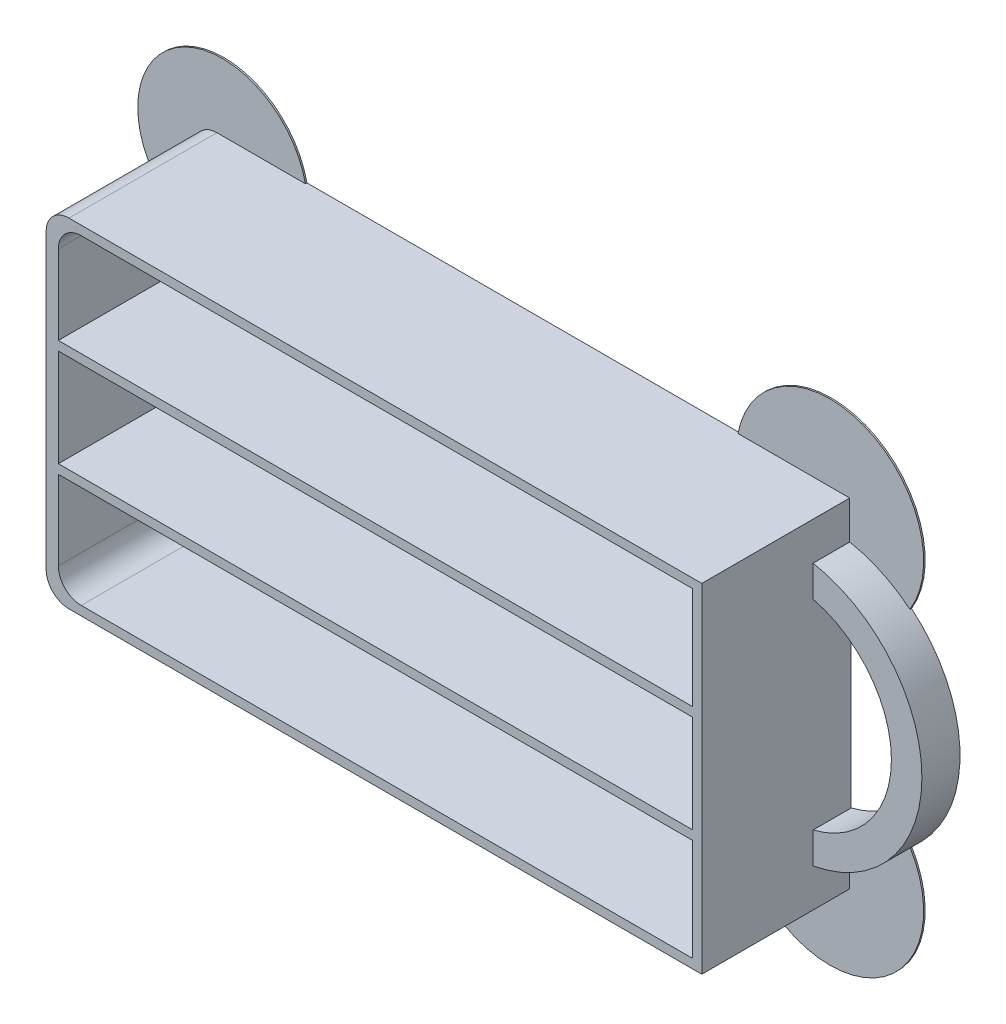
SolidWorks part; units mm, degrees
ref_plane "Спереди" through (0, 0, 0) normal (0, 0, 1) x (1, 0, 0)
ref_plane "Сверху" through (0, 0, 0) normal (0, 1, 0) x (1, 0, 0)
ref_plane "Справа" through (0, 0, 0) normal (1, 0, 0) x (0, 0, -1)
other "Configuration Table"
sketch "Эскиз1" plane through (0, 0, 0) normal (0, 0, 1) x (1, 0, 0)
  line L1 (-43, 22.2) -> (43, 22.2)
  line L2 (-43, 22.2) -> (-43, -22.2)
  line L3 (-43, -22.2) -> (43, -22.2)
  line L4 (43, 22.2) -> (43, -22.2)
  line L5 (-43, 22.2) -> (43, -22.2) construction
  line L6 (-43, -22.2) -> (43, 22.2) construction
  point P0 (0, 0)
  dimension "D1" = 86
  dimension "D2" = 44.4
extrude "Бобышка-Вытянуть1" add sketch "Эскиз1" along normal blind 19.6
sketch "Эскиз2" plane through (0, 0, 0) normal (0, 0, 1) x (1, 0, 0)
  line L0 (0, 0) -> (43, 0) construction
  line L1 (43, -22.2) -> (43, 22.2) construction
  line L2 (43, 17.2) -> (43, 13.1088)
  line L3 (43, -17.2) -> (43, -13.1088)
  arc A0 (43, -17.2) -> (43, 17.2) centre (39.7735, 0) ccw
  arc A1 (43, -13.1088) -> (43, 13.1088) centre (39.7735, 0) ccw
  dimension "D3" = 13.5
  dimension "D4" = 4
  dimension "D1" = 5
  dimension "D2" = 5
extrude "Бобышка-Вытянуть2" add sketch "Эскиз2" along normal blind 5
sketch "Эскиз3" plane through (0, 0, 19.6) normal (0, 0, 1) x (1, 0, 0)
  line L0 (0.2, -21) -> (0.2, 21) construction
  line L2 (41.8, 7.6) -> (-41.4, 7.6)
  line L3 (41.8, 7.6) -> (41.8, 6.4)
  line L4 (41.8, 6.4) -> (-41.4, 6.4)
  line L5 (-41.4, 22.2) -> (-41.4, -22.2)
  line L6 (-43, -21) -> (41.8, -21)
  line L7 (41.8, -21) -> (41.8, 21)
  line L8 (41.8, 21) -> (-43, 21)
  line L9 (-41.4, -21) -> (41.8, -21)
  line L10 (41.8, -21) -> (41.8, 21)
  line L11 (41.8, 21) -> (-41.4, 21)
  line L12 (-41.4, 21) -> (-41.4, -21)
  line L13 (-41.4, 7.6) -> (-41.4, 6.4)
  line L14 (41.8, 7.6) -> (-41.4, 6.4) construction
  line L15 (41.8, 6.4) -> (-41.4, 7.6) construction
  line L16 (41.8, -7.6) -> (-41.4, -7.6)
  line L17 (41.8, -7.6) -> (41.8, -6.4)
  line L18 (41.8, -6.4) -> (-41.4, -6.4)
  line L19 (-41.4, -7.6) -> (-41.4, -6.4)
  line L20 (41.8, -7.6) -> (-41.4, -6.4) construction
  line L21 (41.8, -6.4) -> (-41.4, -7.6) construction
  point P9 (0.2, 7)
  point P15 (0.2, -7)
  dimension "D3" = 1.2
  dimension "D4" = 1.2
  dimension "D5" = 42
  dimension "D6" = 14
  dimension "D7" = 14
  dimension "D8" = 14
  dimension "D1" = 1.2
  dimension "D2" = 1.6
extrude "Вырез-Вытянуть1" cut sketch "Эскиз3" against normal offset from surface (18.4 mm away) 1.2 contours L11 L12 L2 L10 | L18 L10 L4 L12 | L10 L16 L12 L9 up to face at (48.1368, 0, 0)
fillet "Скругление1" radius 3 4 edges at (-43, 22.2, 9.8) (-43, -22.2, 9.8) (-41.4, -21, 10.4) (-41.4, 21, 10.4)
sketch "Эскиз4" plane through (0, 0, 0) normal (0, 0, -1) x (-1, 0, 0)
  line L0 (-43, 22.2) -> (40, 22.2) construction
  line L1 (-50.9089, 13.5001) -> (-28.3502, 22.2)
  line L2 (43, 19.2) -> (43, -19.2) construction
  line L3 (43, 9.4179) -> (28.3958, 22.2)
  line L4 (50, 0) -> (-50, 0) construction
  line L5 (43, -9.4179) -> (28.3958, -22.2)
  line L6 (-50.9089, -13.5001) -> (-28.3502, -22.2)
  arc A0 (-28.3502, 22.2) -> (-50.9089, 13.5001) centre (-40.4154, 19.8876) ccw
  arc A1 (-43, 17.2) -> (-43, -17.2) centre (-39.7735, 0) ccw construction
  arc A2 (28.3958, 22.2) -> (43, 9.4179) centre (39.2676, 19.8876) cw
  arc A3 (28.3958, -22.2) -> (43, -9.4179) centre (39.2676, -19.8876) ccw
  arc A4 (-28.3502, -22.2) -> (-50.9089, -13.5001) centre (-40.4154, -19.8876) cw
extrude "Бобышка-Вытянуть3" add sketch "Эскиз4" against normal blind 0.2
equation "\"D4@Эскиз3\"=\"D3@Эскиз3\""
equation "\"D6@Эскиз3\"=(\"D5@Эскиз3\"/3)"
equation "\"D7@Эскиз3\"=\"D6@Эскиз3\""
